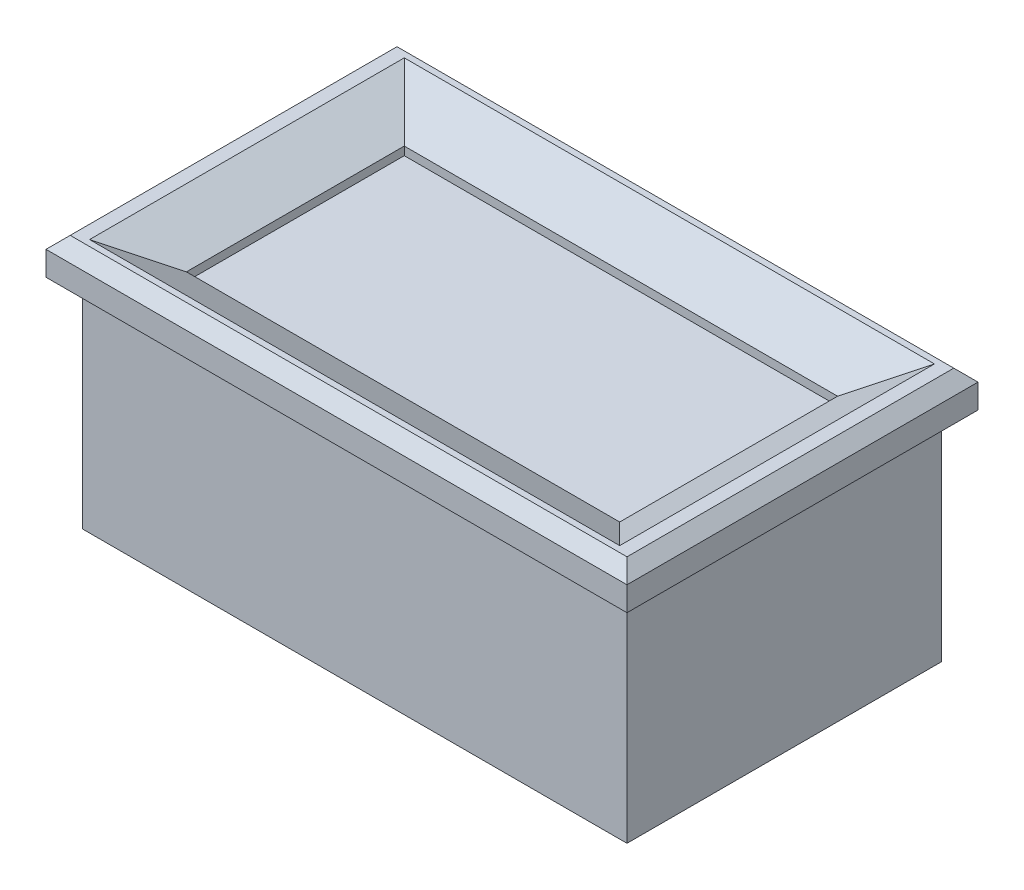
SolidWorks part; units mm, degrees
ref_plane "Front Plane" through (0, 0, 0) normal (0, 0, 1) x (1, 0, 0)
ref_plane "Top Plane" through (0, 0, 0) normal (0, 1, 0) x (1, 0, 0)
ref_plane "Right Plane" through (0, 0, 0) normal (1, 0, 0) x (0, 0, -1)
sketch "Sketch1" plane through (0, 0, 0) normal (0, 1, 0) x (1, 0, 0)
  line L1 (-22.5, -13) -> (22.5, -13)
  line L2 (-22.5, -13) -> (-22.5, 13)
  line L3 (-22.5, 13) -> (22.5, 13)
  line L4 (22.5, -13) -> (22.5, 13)
  line L5 (-22.5, -13) -> (22.5, 13) construction
  line L6 (-22.5, 13) -> (22.5, -13) construction
  point P0 (0, 0)
  dimension "D1" = 26
  dimension "D2" = 45
extrude "Boss-Extrude1" add sketch "Sketch1" along normal blind 18
sketch "Sketch2" plane through (0, 18, 0) normal (0, 1, 0) x (1, 0, 0)
  line L1 (-24, -14.5) -> (24, -14.5)
  line L2 (-24, -14.5) -> (-24, 14.5)
  line L3 (-24, 14.5) -> (24, 14.5)
  line L4 (24, -14.5) -> (24, 14.5)
  line L5 (-24, -14.5) -> (24, 14.5) construction
  line L6 (-24, 14.5) -> (24, -14.5) construction
  line L8 (-17.9, -9) -> (17.9, -9)
  line L10 (-17.9, -9) -> (-17.9, 9)
  line L11 (-17.9, 9) -> (17.9, 9)
  line L12 (17.9, -9) -> (17.9, 9)
  line L13 (-17.9, -9) -> (17.9, 9) construction
  line L14 (-17.9, 9) -> (17.9, -9) construction
  point P0 (0, 0)
  point P6 (0, 0)
  dimension "D1" = 48
  dimension "D2" = 29
  dimension "D3" = 18
  dimension "D4" = 35.8
extrude "Boss-Extrude2" add sketch "Sketch2" along normal blind 3
chamfer "Chamfer1" distance 1 angle 45 4 edges at (0, 21, -14.5) (24, 21, 0) (-24, 21, 0) (0, 21, 14.5)
chamfer "Chamfer2" distance 4 angle 30 4 edges at (17.9, 21, 0) (0, 21, 9) (-17.9, 21, 0) (0, 21, -9)
